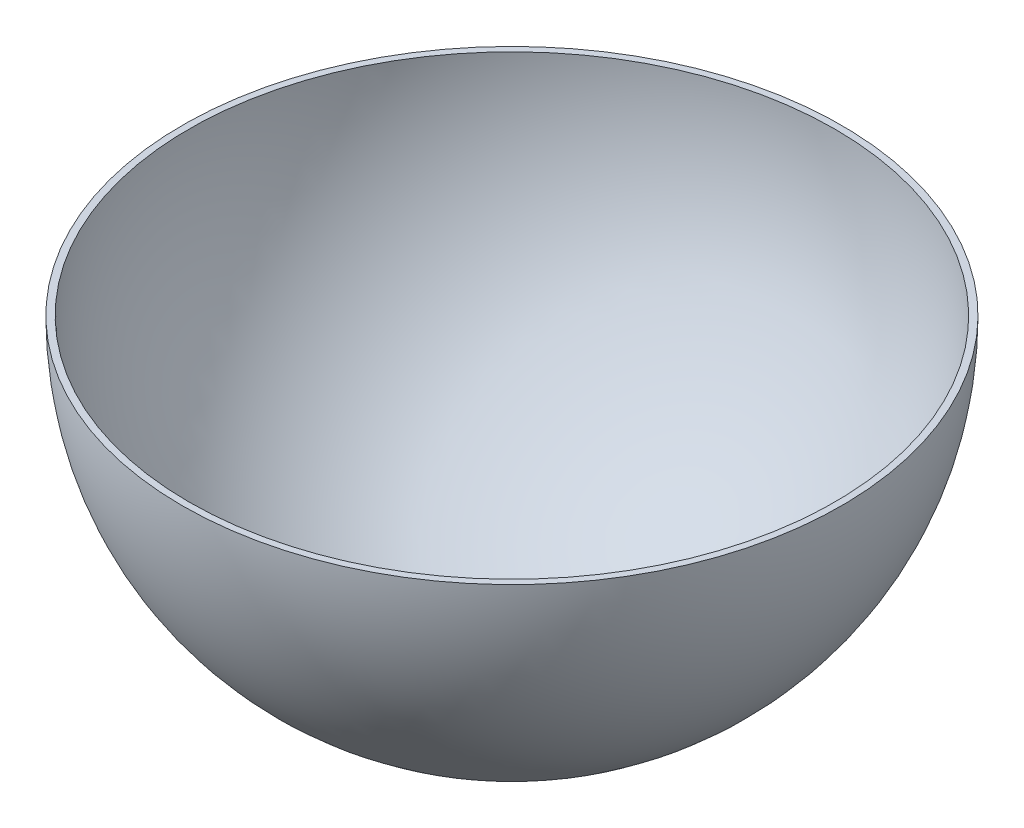
SolidWorks part; units mm, degrees
ref_plane "前视基准面" through (0, 0, 0) normal (0, 0, 1) x (1, 0, 0)
ref_plane "上视基准面" through (0, 0, 0) normal (0, 1, 0) x (1, 0, 0)
ref_plane "右视基准面" through (0, 0, 0) normal (1, 0, 0) x (0, 0, -1)
sketch "草图1" plane through (0, 0, 0) normal (0, 0, 1) x (1, 0, 0)
  line L0 (-100, 0) -> (-98, 0)
  line L1 (98, 0) -> (100, 0)
  arc A0 (-100, 0) -> (100, 0) centre (0, 0) ccw
  arc A1 (-98, 0) -> (98, 0) centre (0, 0) ccw
  dimension "D1" = 200
  dimension "D2" = 196
revolve "旋转1" add sketch "草图1" angle 360 about L0
sketch "草图2" plane through (0, 0, 0) normal (0, 1, 0) x (1, 0, 0)
  circle A0 centre (0, 0) radius 100
extrude "切除-拉伸1" cut sketch "草图2" along normal through all
sketch "草图3" plane through (0, 0, 0) normal (0, 1, 0) x (1, 0, 0)
  circle A0 centre (0, 0) radius 2.5
  dimension "D1" = 5
extrude "切除-拉伸2" cut sketch "草图3" against normal through all
